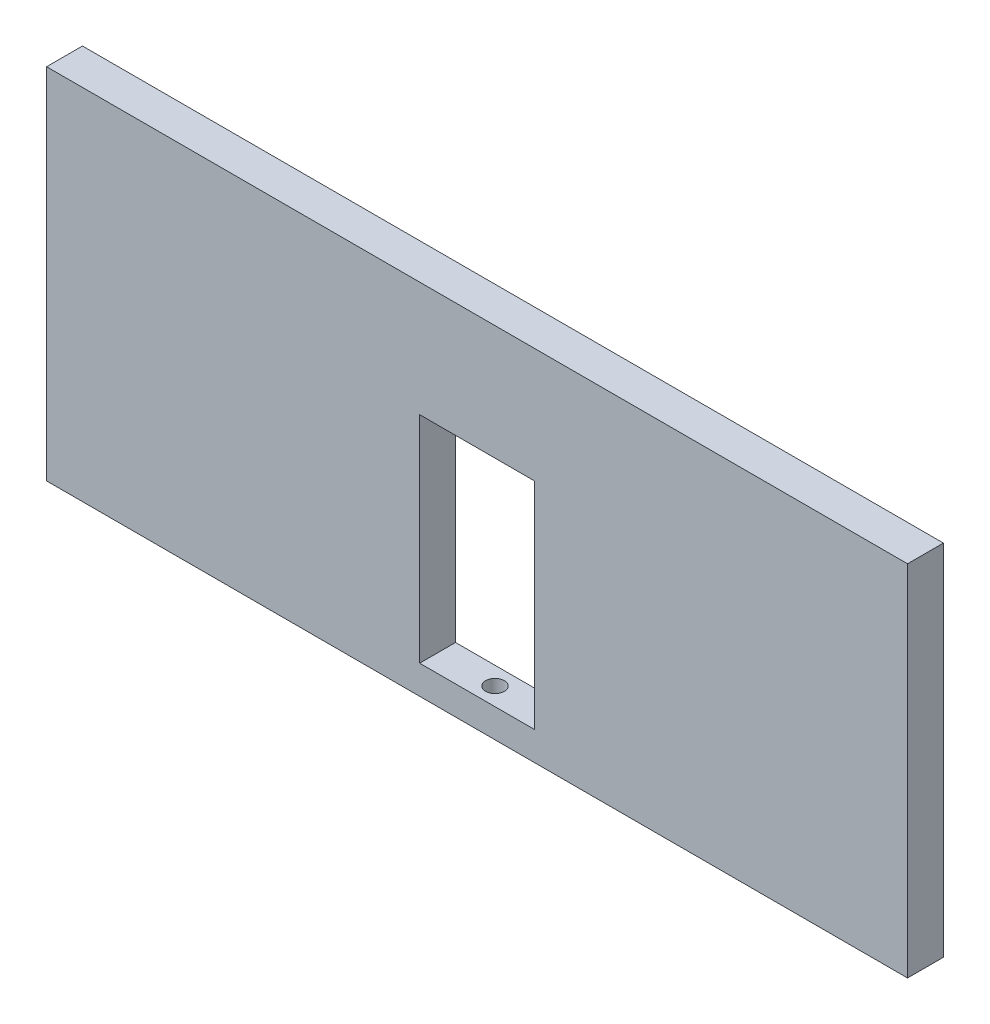
SolidWorks part; units mm, degrees
ref_plane "Alzado" through (0, 0, 0) normal (0, 0, 1) x (1, 0, 0)
ref_plane "Planta" through (0, 0, 0) normal (0, 1, 0) x (1, 0, 0)
ref_plane "Vista lateral" through (0, 0, 0) normal (1, 0, 0) x (0, 0, -1)
sketch "Croquis1" plane through (0, 0, 0) normal (0, 0, 1) x (1, 0, 0)
  line L0 (0, -125) -> (0, -105) construction
  line L1 (-40, -105) -> (40, -105)
  line L3 (-300, -125) -> (300, -125)
  line L6 (-300, -125) -> (-300, 125)
  line L7 (-300, 125) -> (300, 125)
  line L8 (-40, -105) -> (-40, 45)
  line L10 (300, -125) -> (300, 125)
  line L12 (40, -105) -> (40, 45)
  line L15 (40, 45) -> (-40, 45)
  line L17 (-300, -125) -> (300, 125) construction
  point P4 (0, 0)
  dimension "D1" = 20
  dimension "D2" = 600
  dimension "D3" = 80
  dimension "D4" = 150
  dimension "D5" = 250
extrude "Saliente-Extruir2" add sketch "Croquis1" along normal blind 25
sketch "Croquis3" plane through (0, -125, 0) normal (0, -1, 0) x (1, 0, 0)
  line L0 (-300, 0) -> (300, 25) construction
  circle A0 centre (0, 12.5) radius 6.5
  dimension "D1" = 13
extrude "Cortar-Extruir2" cut sketch "Croquis3" against normal up to next
